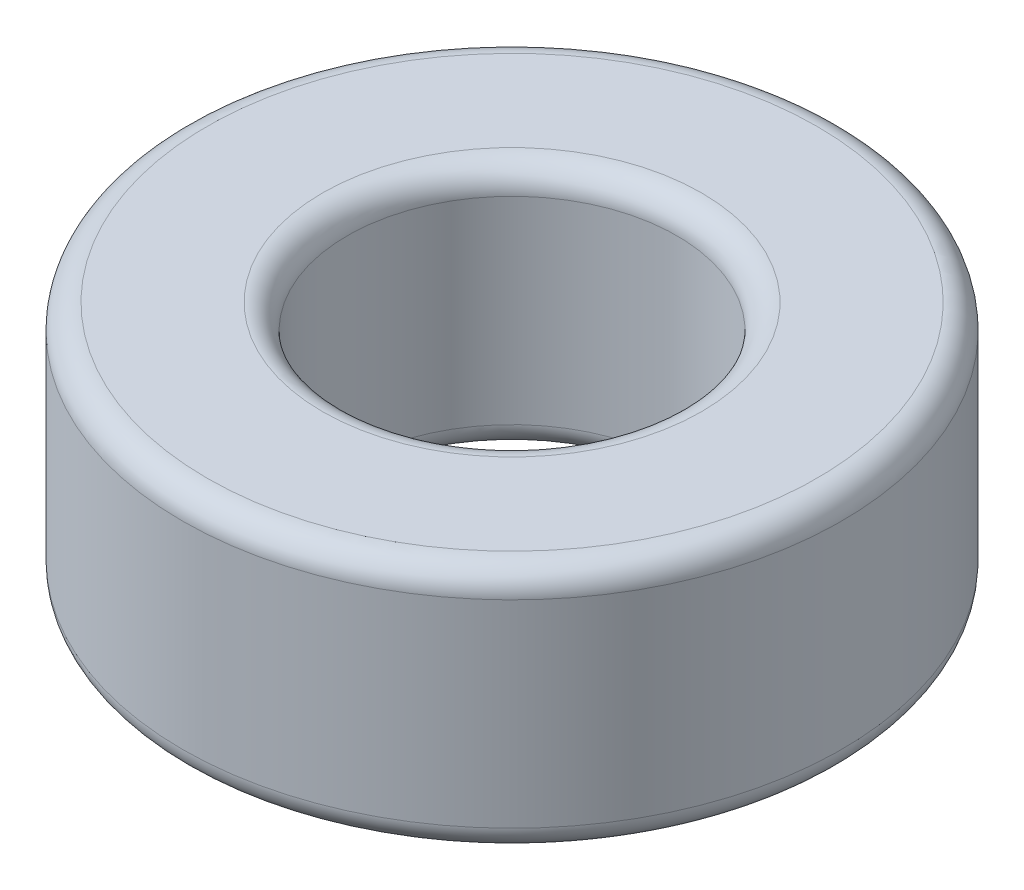
SolidWorks part; units mm, degrees
material "Cast Alloy Steel"
ref_plane "Front Plane" through (0, 0, 0) normal (0, 0, 1) x (1, 0, 0)
ref_plane "Top Plane" through (0, 0, 0) normal (0, 1, 0) x (1, 0, 0)
ref_plane "Right Plane" through (0, 0, 0) normal (1, 0, 0) x (0, 0, -1)
sketch "Sketch1" plane through (0, 0, 0) normal (0, 1, 0) x (1, 0, 0)
  circle A0 centre (0, 0) radius 3.175
  circle A1 centre (0, 0) radius 6.35
  dimension "ID" = 6.35
  dimension "OD" = 12.7
extrude "Bore" add sketch "Sketch1" along normal blind 4.7625
fillet "Fillet" radius 0.4763 4 edges at (0, 4.7625, 3.175) (0, 4.7625, 6.35) (0, 0, 3.175) (0, 0, 6.35)
equation "\"ID@Sketch1\"  = .25in"
equation "\"OD@Sketch1\"  = .5in"
equation "\"D1@Bore\" = .1875in"
equation "\"D1@Fillet\"= \"D1@Bore\" / 10"
